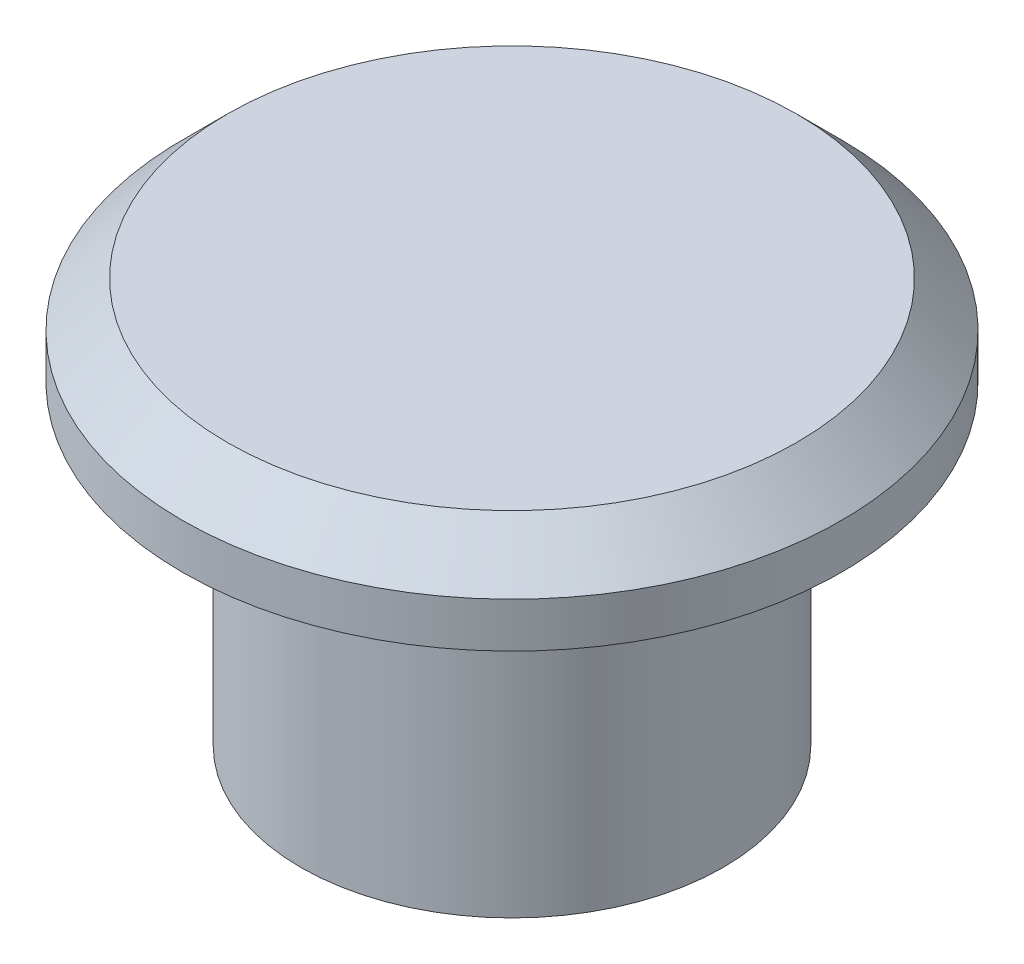
SolidWorks part; units mm, degrees
ref_plane "Front Plane" through (0, 0, 0) normal (0, 0, 1) x (1, 0, 0)
ref_plane "Top Plane" through (0, 0, 0) normal (0, 1, 0) x (1, 0, 0)
ref_plane "Right Plane" through (0, 0, 0) normal (1, 0, 0) x (0, 0, -1)
sketch "Sketch1" plane through (0, 0, 0) normal (0, 1, 0) x (1, 0, 0)
  circle A0 centre (0, 0) radius 4.7
extrude "Boss-Extrude1" add sketch "Sketch1" along normal blind 7
sketch "Sketch2" plane through (0, 7, 0) normal (0, 1, 0) x (-1, 0, 0)
  circle A0 centre (0, 0) radius 3.507
extrude "Cut-Extrude1" cut sketch "Sketch2" against normal blind 7
sketch "Sketch3" plane through (0, 7, 0) normal (0, 1, 0) x (1, 0, 0)
  circle A0 centre (0, 0) radius 7.3307
extrude "Boss-Extrude2" add sketch "Sketch3" along normal blind 2
chamfer "Chamfer1" distance 1 angle 45 1 edges at (0, 9, 7.3307)
